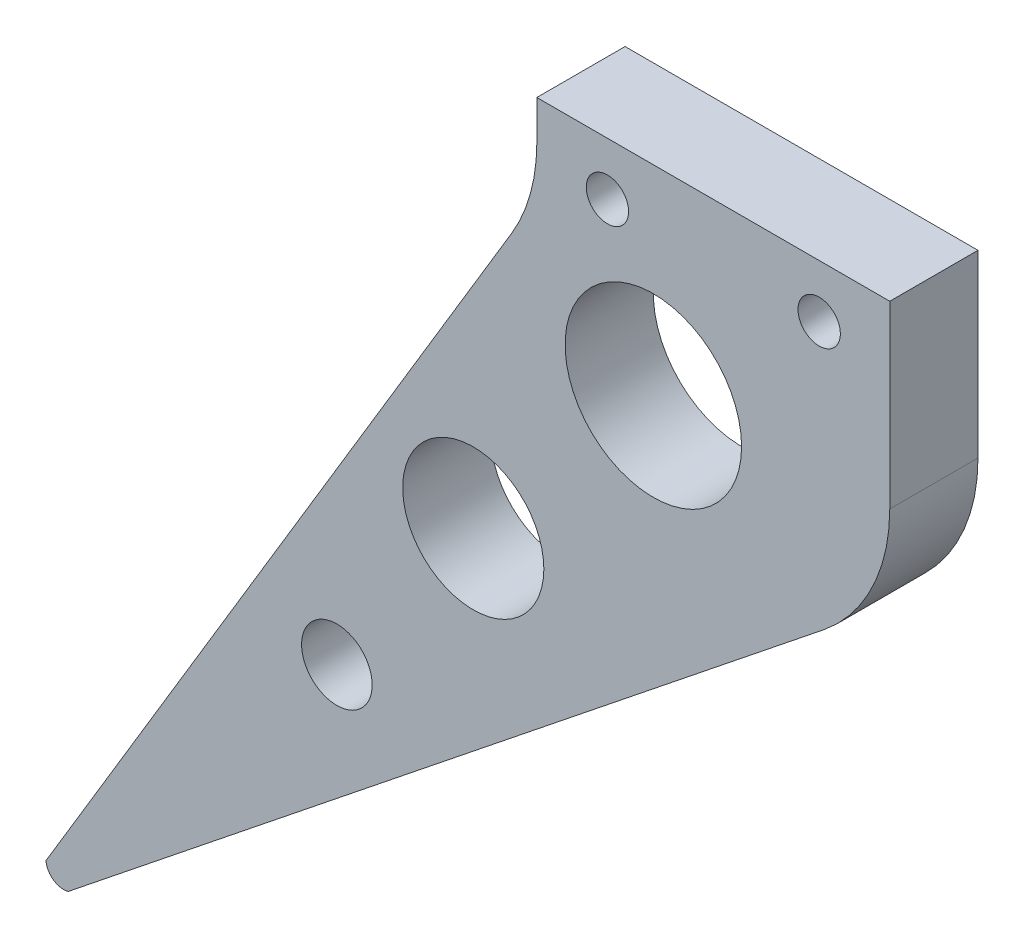
SolidWorks part; units mm, degrees
ref_plane "Plan de face" through (0, 0, 0) normal (0, 0, 1) x (1, 0, 0)
ref_plane "Plan de dessus" through (0, 0, 0) normal (0, 1, 0) x (1, 0, 0)
ref_plane "Plan de droite" through (0, 0, 0) normal (1, 0, 0) x (0, 0, -1)
sketch "Esquisse1" plane through (0, 0, 0) normal (0, 0, 1) x (1, 0, 0)
  line L0 (0, 0) -> (30, 50)
  line L1 (30, 50) -> (50, 50)
  line L2 (50, 50) -> (50, 40)
  line L3 (50, 40) -> (0, 0)
  line L4 (50, 50) -> (0, 0) construction
  circle A0 centre (36.6024, 43.6734) radius 5
  circle A1 centre (26.3975, 32.0543) radius 4
  circle A2 centre (18.6684, 21.4968) radius 2
  dimension "D5" = 10
  dimension "D6" = 8
  dimension "D7" = 4
  dimension "D1" = 20
  dimension "D2" = 10
  dimension "D3" = 50
  dimension "D4" = 50
extrude "Boss.-Extru.1" add sketch "Esquisse1" along normal blind 5
sketch "Esquisse2" plane through (0, 0, 0) normal (0, 0, -1) x (-1, 0, 0)
  line L0 (-30, 50) -> (0, 0) construction
  line L1 (0, 0) -> (-50, 40) construction
  arc A0 (-2.1857, 3.6428) -> (-4.0658, 3.2526) centre (-3.1826, 3.7216) cw
  dimension "D1" = 1
extrude "Enlèv. mat.-Extru.1" cut sketch "Esquisse2" against normal blind 5 and the other way through all
fillet "Congé1" radius 10 1 edges at (50, 40, 2.5)
sketch "Esquisse3" plane through (0, 50, 0) normal (0, 1, 0) x (1, 0, 0)
  line L1 (30, 0) -> (50, 0)
  line L2 (30, 0) -> (30, -5)
  line L3 (30, -5) -> (50, -5)
  line L4 (50, 0) -> (50, -5)
extrude "Boss.-Extru.2" add sketch "Esquisse3" along normal blind 5
hole_wizard "Dégagement M21" positions "Esquisse4" profile "Esquisse5" size "M2" standard "ISO" slot yes end condition up to next
sketch "Esquisse4" plane through (0, 0, 5) normal (0, 0, 1) x (1, 0, 0)
  line L0 (30, 55) -> (30, 50) construction
  line L1 (50, 44.8062) -> (50, 55) construction
  line L2 (30, 55) -> (50, 55) construction
  point P0 (46, 52)
  point P2 (34, 52)
  dimension "D1" = 4
  dimension "D2" = 4
  dimension "D3" = 3
  dimension "D4" = 3
sketch "Esquisse5" plane through (46, 52, 5) normal (1, 0, 0) x (0, -1, 0)
  line L0 (0, 0) -> (0, 5)
  line L1 (0, 5) -> (1.2, 5)
  line L2 (1.2, 5) -> (1.2, 0)
  line L5 (1.2, 0) -> (0, 0)
  line L11 (0, -6.35) -> (0, 107.95) construction
  dimension "Diamètre du perçage jusqu'au prochain" = 2.4
  dimension "Profondeur du perçage jusqu'au prochain" = 5
fillet "Congé2" radius 10 1 edges at (30, 50, 2.5)
